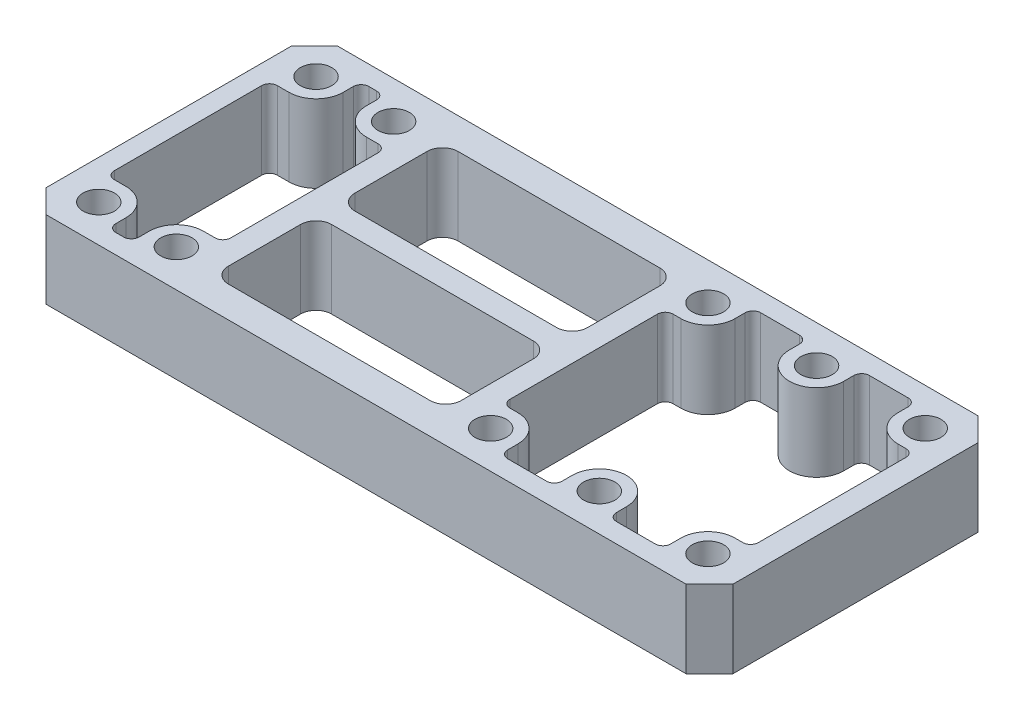
SolidWorks part; units mm, degrees
material "6061-T6 (SS)"
ref_plane "前视基准面" through (0, 0, 0) normal (0, 0, 1) x (1, 0, 0)
ref_plane "上视基准面" through (0, 0, 0) normal (0, 1, 0) x (1, 0, 0)
ref_plane "右视基准面" through (0, 0, 0) normal (1, 0, 0) x (0, 0, -1)
sketch "草图1" plane through (0, 0, 0) normal (0, 1, 0) x (1, 0, 0)
  line L1 (-5, 14) -> (5, 14) construction
  line L2 (-5, 14) -> (-5, -14) construction
  line L3 (-5, -14) -> (5, -14) construction
  line L4 (5, 14) -> (5, -14) construction
  line L5 (0, -14) -> (0, 14) construction
  line L6 (-5, 0) -> (5, 0) construction
  line L7 (45.5, 14) -> (73.5, 14) construction
  line L8 (45.5, 14) -> (45.5, -14) construction
  line L9 (45.5, -14) -> (73.5, -14) construction
  line L10 (73.5, 14) -> (73.5, -14) construction
  line L11 (59.5, -14) -> (59.5, 14) construction
  line L12 (45.5, 0) -> (73.5, 0) construction
  line L13 (-10, 18.8) -> (78.5, 18.8)
  line L14 (-10, 18.8) -> (-10, -18.8)
  line L15 (-10, -18.8) -> (78.5, -18.8)
  line L16 (78.5, 18.8) -> (78.5, -18.8)
  line L17 (34.25, -18.8) -> (34.25, 18.8) construction
  line L18 (-10, 0) -> (78.5, 0) construction
  circle A0 centre (-5, 14) radius 2.025
  circle A1 centre (5, 14) radius 2.025
  circle A2 centre (5, -14) radius 2.025
  circle A3 centre (-5, -14) radius 2.025
  circle A4 centre (45.5, 14) radius 2.025
  circle A5 centre (59.5, 14) radius 2.025
  circle A6 centre (73.5, 14) radius 2.025
  circle A7 centre (73.5, -14) radius 2.025
  circle A8 centre (59.5, -14) radius 2.025
  circle A9 centre (45.5, -14) radius 2.025
  point P0 (0, 0)
  point P4 (59.5, 0)
  point P179 (34.25, 0)
  dimension "D6" = 4.05
  dimension "D1" = 28
  dimension "D2" = 10
  dimension "D3" = 28
  dimension "D4" = 28
  dimension "D5" = 59.5
  dimension "D7" = 5
  dimension "D8" = 4.8
  dimension "D9" = 5
extrude "凸台-拉伸1" add sketch "草图1" along normal blind 10
sketch "草图2" plane through (0, 10, 0) normal (0, 1, 0) x (1, 0, 0)
  line L0 (0, 0) -> (49488.671, 0) construction
  line L1 (-5, 14) -> (5, 14) construction
  line L2 (-5, 14) -> (-5, -14) construction
  line L3 (-5, -14) -> (5, -14) construction
  line L4 (5, 14) -> (5, -14) construction
  line L5 (0, -14) -> (0, 14) construction
  line L6 (-5, 0) -> (5, 0) construction
  line L7 (0, 0) -> (0, -49976.4929) construction
  line L8 (-7.5, -9.5) -> (-7.5, 9.5)
  line L9 (-6.5, 10.5) -> (-5, 10.5)
  line L10 (-1.5, 14) -> (-1.5, 15.3)
  line L11 (-0.5, 16.3) -> (0.5, 16.3)
  line L12 (-10, 18.8) -> (-10, -18.8) construction
  line L13 (78.5, 18.8) -> (-10, 18.8) construction
  line L14 (-0.5, -16.3) -> (0.5, -16.3)
  line L15 (-1.5, -14) -> (-1.5, -15.3)
  line L16 (-6.5, -10.5) -> (-5, -10.5)
  line L17 (1.5, -14) -> (1.5, -15.3)
  line L18 (6.5, -10.5) -> (5, -10.5)
  line L19 (7.5, -9.5) -> (7.5, 9.5)
  line L20 (6.5, 10.5) -> (5, 10.5)
  line L21 (1.5, 14) -> (1.5, 15.3)
  arc A0 (-7.5, 9.5) -> (-6.5, 10.5) centre (-6.5, 9.5) cw
  arc A1 (-5, 10.5) -> (-1.5, 14) centre (-5, 14) ccw
  arc A2 (-1.5, 15.3) -> (-0.5, 16.3) centre (-0.5, 15.3) cw
  arc A3 (-1.5, -15.3) -> (-0.5, -16.3) centre (-0.5, -15.3) ccw
  arc A4 (-5, -10.5) -> (-1.5, -14) centre (-5, -14) cw
  arc A5 (-7.5, -9.5) -> (-6.5, -10.5) centre (-6.5, -9.5) ccw
  arc A6 (1.5, -15.3) -> (0.5, -16.3) centre (0.5, -15.3) cw
  arc A7 (5, -10.5) -> (1.5, -14) centre (5, -14) ccw
  arc A8 (7.5, -9.5) -> (6.5, -10.5) centre (6.5, -9.5) cw
  arc A9 (7.5, 9.5) -> (6.5, 10.5) centre (6.5, 9.5) ccw
  arc A10 (5, 10.5) -> (1.5, 14) centre (5, 14) cw
  arc A11 (1.5, 15.3) -> (0.5, 16.3) centre (0.5, 15.3) ccw
  point P31 (-7.5, 0)
  point P32 (0, -16.3)
  point P47 (0, 16.3)
  point P108 (0, 0)
  dimension "D1" = 1
  dimension "D2" = 3.5
  dimension "D3" = 2.5
  dimension "D4" = 2.5
extrude "切除-拉伸1" cut sketch "草图2" against normal through all
sketch "草图3" plane through (0, 0, 0) normal (0, -1, 0) x (1, 0, 0)
  line L0 (67, 0) -> (49927.1545, 0) construction
  line L1 (45.5, 14) -> (73.5, 14) construction
  line L2 (45.5, 14) -> (45.5, -14) construction
  line L3 (45.5, -14) -> (73.5, -14) construction
  line L4 (73.5, 14) -> (73.5, -14) construction
  line L5 (59.5, -14) -> (59.5, 14) construction
  line L6 (45.5, 0) -> (73.5, 0) construction
  line L7 (43.5, -9.5) -> (43.5, 9.5)
  line L8 (44.5, 10.5) -> (45.5, 10.5)
  line L9 (49, 14) -> (49, 15.3)
  line L10 (50, 16.3) -> (55, 16.3)
  line L11 (56, 15.3) -> (56, 14)
  line L12 (-10, 18.8) -> (78.5, 18.8) construction
  line L13 (56, -15.3) -> (56, -14)
  line L14 (50, -16.3) -> (55, -16.3)
  line L15 (49, -14) -> (49, -15.3)
  line L16 (44.5, -10.5) -> (45.5, -10.5)
  line L17 (63, -15.3) -> (63, -14)
  line L18 (69, -16.3) -> (64, -16.3)
  line L19 (70, -14) -> (70, -15.3)
  line L20 (74.5, -10.5) -> (73.5, -10.5)
  line L21 (75.5, -9.5) -> (75.5, 9.5)
  line L22 (74.5, 10.5) -> (73.5, 10.5)
  line L23 (70, 14) -> (70, 15.3)
  line L24 (69, 16.3) -> (64, 16.3)
  line L25 (63, 15.3) -> (63, 14)
  arc A0 (43.5, 9.5) -> (44.5, 10.5) centre (44.5, 9.5) cw
  arc A1 (45.5, 10.5) -> (49, 14) centre (45.5, 14) ccw
  arc A2 (49, 15.3) -> (50, 16.3) centre (50, 15.3) cw
  arc A3 (55, 16.3) -> (56, 15.3) centre (55, 15.3) cw
  arc A4 (56, 14) -> (63, 14) centre (59.5, 14) ccw
  arc A5 (56, -14) -> (63, -14) centre (59.5, -14) cw
  arc A6 (55, -16.3) -> (56, -15.3) centre (55, -15.3) ccw
  arc A7 (49, -15.3) -> (50, -16.3) centre (50, -15.3) ccw
  arc A8 (45.5, -10.5) -> (49, -14) centre (45.5, -14) cw
  arc A9 (43.5, -9.5) -> (44.5, -10.5) centre (44.5, -9.5) ccw
  arc A10 (64, -16.3) -> (63, -15.3) centre (64, -15.3) cw
  arc A11 (70, -15.3) -> (69, -16.3) centre (69, -15.3) cw
  arc A12 (73.5, -10.5) -> (70, -14) centre (73.5, -14) ccw
  arc A13 (75.5, -9.5) -> (74.5, -10.5) centre (74.5, -9.5) cw
  arc A14 (75.5, 9.5) -> (74.5, 10.5) centre (74.5, 9.5) ccw
  arc A15 (73.5, 10.5) -> (70, 14) centre (73.5, 14) cw
  arc A16 (70, 15.3) -> (69, 16.3) centre (69, 15.3) ccw
  arc A17 (64, 16.3) -> (63, 15.3) centre (64, 15.3) ccw
  point P40 (43.5, 0)
  point P188 (59.5, 0)
  dimension "D3" = 1
  dimension "D4" = 3.5
  dimension "D1" = 2
  dimension "D2" = 2.5
extrude "切除-拉伸2" cut sketch "草图3" against normal through all
sketch "草图4" plane through (0, 0, 0) normal (0, -1, 0) x (1, 0, 0)
  line L0 (0, 0) -> (-50000, 0) construction
  line L1 (7.5, 9.5) -> (43.5, 9.5) construction
  line L2 (25.5, 9.5) -> (25.5, -49990.5) construction
  line L3 (-10, 18.8) -> (78.5, 18.8) construction
  line L4 (10.5, 14.8) -> (40.5, 14.8)
  line L5 (10.5, 14.8) -> (10.5, -14.8)
  line L6 (10.5, -14.8) -> (40.5, -14.8)
  line L7 (40.5, 14.8) -> (40.5, -14.8)
  line L8 (25.5, -14.8) -> (25.5, 14.8) construction
  line L9 (10.5, 0) -> (40.5, 0) construction
  line L10 (7.5, 9.5) -> (7.5, -9.5) construction
  point P9 (25.5, 9.5)
  point P10 (25.5, 0)
  dimension "D1" = 4
  dimension "D2" = 3
extrude "切除-拉伸3" cut sketch "草图4" against normal through all
sketch "草图5" plane through (0, 0, 0) normal (0, -1, 0) x (1, 0, 0)
  line L0 (0, 0) -> (-50000, 0) construction
  line L1 (10.5, 14.8) -> (10.5, -14.8) construction
  line L2 (10.5, 1.5) -> (40.5, 1.5)
  line L3 (10.5, 1.5) -> (10.5, -1.5)
  line L4 (10.5, -1.5) -> (40.5, -1.5)
  line L5 (40.5, 1.5) -> (40.5, -1.5)
  line L6 (25.5, -1.5) -> (25.5, 1.5) construction
  line L7 (10.5, 0) -> (40.5, 0) construction
  line L8 (40.5, -14.8) -> (40.5, 14.8) construction
  point P155 (25.5, 0)
  dimension "3" = 3
extrude "凸台-拉伸2" add sketch "草图5" against normal up to surface (10 mm away) up to face at (25.5, 10, 0)
fillet "圆角1" radius 2 8 edges at (10.5, 5, 14.8) (10.5, 5, 1.5) (10.5, 5, -1.5) (10.5, 5, -14.8) (40.5, 5, -14.8) (40.5, 5, -1.5) (40.5, 5, 1.5) (40.5, 5, 14.8)
chamfer "倒角1" distance 3 angle 45 4 edges at (78.5, 5, -18.8) (78.5, 5, 18.8) (-10, 5, 18.8) (-10, 5, -18.8)
